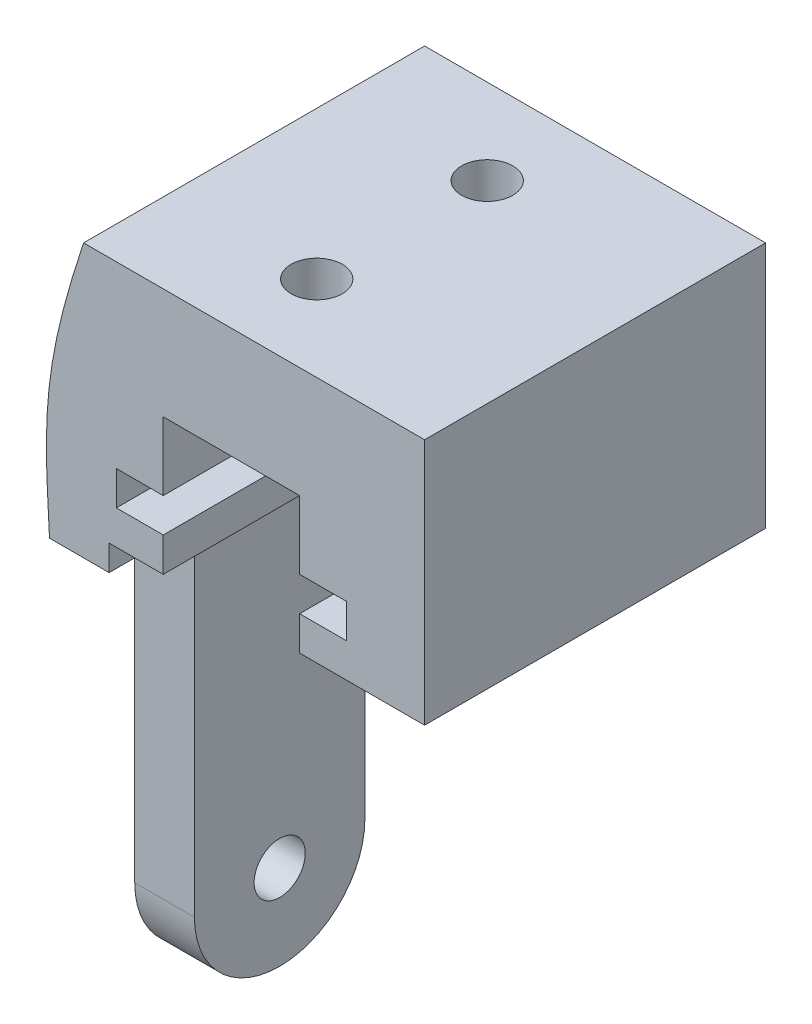
SolidWorks part; units mm, degrees
ref_plane "Front Plane" through (0, 0, 0) normal (0, 0, 1) x (1, 0, 0)
ref_plane "Top Plane" through (0, 0, 0) normal (0, 1, 0) x (1, 0, 0)
ref_plane "Right Plane" through (0, 0, 0) normal (1, 0, 0) x (0, 0, -1)
sketch "Sketch1" plane through (0, 0, 0) normal (0, 0, 1) x (1, 0, 0)
  line L0 (-10, 0) -> (10, 0)
  line L1 (-12, -16) -> (12, -16) construction
  line L2 (0, 2.1893) -> (0, -16.9572) construction
  line L3 (-8.5, -16) -> (-8.5, -14.5)
  line L4 (-8.5, -14.5) -> (-5.328, -14.5)
  line L5 (-5.328, -14.5) -> (-5.328, -12.5)
  line L6 (-5.328, -12.5) -> (-8.078, -12.5)
  line L7 (-8.078, -12.5) -> (-8.078, -10.5)
  line L8 (-8.078, -10.5) -> (-5.328, -10.5)
  line L9 (-5.328, -10.5) -> (-5.328, -6.5)
  line L10 (-5.328, -6.5) -> (2.672, -6.5)
  line L11 (2.672, -6.5) -> (2.672, -10.5)
  line L12 (2.672, -10.5) -> (5.422, -10.5)
  line L13 (5.422, -10.5) -> (5.422, -12.5)
  line L14 (5.422, -12.5) -> (2.672, -12.5)
  line L15 (2.672, -12.5) -> (2.672, -14.5)
  line L16 (2.672, -14.5) -> (10, -14.5)
  line L17 (10, 0) -> (10, -14.5)
  line L18 (-12, -16) -> (-8.5, -16)
  spline S0 degree 3 poles (-10, 0) (-12.5766, -7.7406) (-12.2843, -10.4924) (-12, -16) knots 0 0 0 0 1 1 1 1
  point P5 (0, -16)
  dimension "D1" = 20
  dimension "D2" = 24
  dimension "D3" = 16
  dimension "D4" = 13.5
  dimension "D5" = 2
  dimension "D6" = 8
  dimension "D7" = 4
  dimension "D8" = 1.5
  dimension "D9" = 3.5
  dimension "D10" = 6.5
  dimension "D11" = 2.75
extrude "Boss-Extrude1" add sketch "Sketch1" along normal blind 20 contours S0 L18 L3 L4 L5 L6 L7 L8 L9 L10 L11 L12 L13 L14 L15 L16 L17 L0
sketch "Sketch2" plane through (0, -6.5, 0) normal (0, -1, 0) x (1, 0, 0)
  line L0 (-1.328, 20) -> (-1.328, -1.2502) construction
  line L1 (-5.328, 20) -> (2.672, 20) construction
  line L2 (-5.328, 0) -> (2.672, 0) construction
  circle A0 centre (-1.328, 15) radius 1.5
  circle A1 centre (-1.328, 5) radius 1.5
  dimension "D1" = 3
  dimension "D2" = 5
  dimension "D3" = 5
extrude "Cut-Extrude1" cut sketch "Sketch2" against normal up to surface (6.5 mm away) up to face at (0, 0, 10)
sketch "Sketch4" plane through (0, -16, 0) normal (0, -1, 0) x (1, 0, 0)
  line L0 (-12, 20) -> (-12, 0) construction
  line L1 (-12, 15) -> (-8.5, 15)
  line L2 (-12, 15) -> (-12, 5)
  line L3 (-12, 5) -> (-8.5, 5)
  line L4 (-8.5, 15) -> (-8.5, 5)
  line L5 (-8.5, 20) -> (-8.5, 0) construction
  dimension "D1" = 10
  dimension "D2" = 5
extrude "Boss-Extrude2" add sketch "Sketch4" along normal blind 20
sketch "Sketch5" plane through (-12, 0, 0) normal (-1, 0, 0) x (0, 0, 1)
  line L4 (15, -16) -> (5, -16)
  line L5 (5, -16) -> (5, -36)
  line L6 (5, -36) -> (15, -36)
  line L7 (15, -36) -> (15, -16)
  line L10 (5, -36) -> (15, -36)
  arc A0 (5, -36) -> (15, -36) centre (10, -36) ccw
  dimension "D1" = 0
extrude "Boss-Extrude3" add sketch "Sketch5" against normal up to surface (3.5 mm away) up to face at (-8.5, -23.125, 10.625)
sketch "Sketch6" plane through (-12, 0, 0) normal (-1, 0, 0) x (0, 0, 1)
  line L0 (10, -41) -> (10, -34.3296) construction
  line L1 (5, -36) -> (15, -36) construction
  circle A0 centre (10, -36) radius 1.5
  arc A1 (5, -36) -> (15, -36) centre (10, -36) ccw construction
  dimension "D1" = 3
extrude "Cut-Extrude2" cut sketch "Sketch6" against normal blind 20
